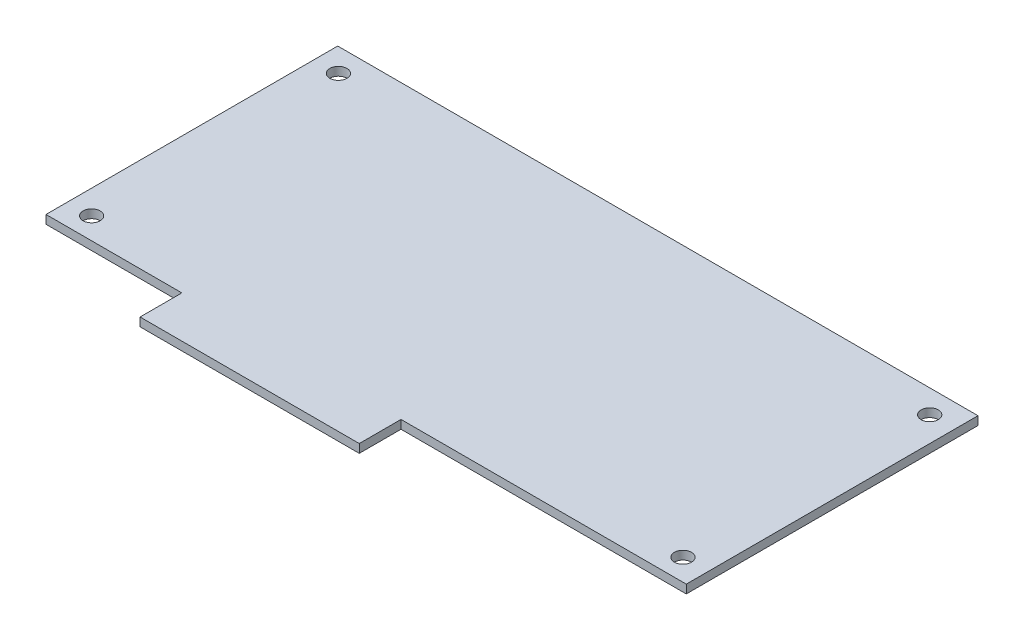
SolidWorks part; units mm, degrees
ref_plane "Front Plane" through (0, 0, 0) normal (0, 0, 1) x (1, 0, 0)
ref_plane "Top Plane" through (0, 0, 0) normal (0, 1, 0) x (1, 0, 0)
ref_plane "Right Plane" through (0, 0, 0) normal (1, 0, 0) x (0, 0, -1)
sketch "Sketch1" plane through (0, 0, 0) normal (0, 1, 0) x (1, 0, 0)
  line L0 (19.558, 31.75) -> (19.558, 36.2756)
  line L1 (60.96, -31.75) -> (-60.96, -31.75)
  line L2 (60.96, -31.75) -> (60.96, 31.75)
  line L3 (60.96, 31.75) -> (-60.96, 31.75)
  line L4 (-60.96, -31.75) -> (-60.96, 31.75)
  line L5 (60.96, -31.75) -> (-60.96, 31.75) construction
  line L6 (60.96, 31.75) -> (-60.96, -31.75) construction
  line L7 (19.558, 36.2756) -> (-17.272, 36.2756)
  line L8 (-17.272, 36.2756) -> (-17.272, 31.75)
  line L9 (1.143, 36.2756) -> (1.143, 31.75) construction
  line L10 (-60.96, -23.7998) -> (-35.092, -23.7998)
  line L11 (-35.092, -23.7998) -> (-35.092, -31.75)
  line L12 (60.96, -23.7998) -> (6.6402, -23.7998)
  line L13 (6.6402, -23.7998) -> (6.6402, -31.75)
  point P0 (0, 0)
  dimension "D1" = 121.92
  dimension "D2" = 63.5
  dimension "D3" = 36.83
  dimension "D4" = 4.5256
  dimension "D5" = 59.817
  dimension "D6" = 55.5498
  dimension "D7" = 41.7322
  dimension "D8" = 25.868
extrude "Boss-Extrude1" add sketch "Sketch1" along normal blind 1.6256 contours L13 L12 L2 L3 L4 L10 L11 L1
hole_wizard "#4 Clearance Hole1" positions "Sketch3" profile "Sketch2" hole size "#4" standard "ANSI Inch"
sketch "Sketch3" plane through (-46.7013, 0, 29.5549) normal (0, -1, 0) x (-1, 0, 0)
  line L1 (9.6867, 56.8599) -> (-102.9115, 56.8599)
  line L2 (9.6867, 9.8699) -> (-102.9115, 9.8699)
  line L6 (-107.6613, 61.3049) -> (14.2587, 61.3049) construction
  line L7 (14.2587, -2.1951) -> (14.2587, 61.3049) construction
  line L9 (-107.6613, -2.1951) -> (-107.6613, 61.3049) construction
  line L10 (-107.6613, 5.7551) -> (-53.3415, 5.7551) construction
  point P9 (-102.9115, 9.8699)
  point P10 (-102.9115, 56.8599)
  point P11 (9.6867, 56.8599)
  point P12 (9.6867, 9.8699)
  dimension "D1" = 4.572
  dimension "D2" = 46.99
  dimension "D3" = 4.7498
  dimension "D4" = 4.445
  dimension "D5" = 4.1148
sketch "Sketch2" plane through (56.2102, 0, 19.685) normal (1, 0, 0) x (0, 0, -1)
  line L0 (0, 0) -> (0, 57.3686)
  line L1 (0, 57.3686) -> (1.6319, 56.388)
  line L2 (1.6319, 56.388) -> (1.6319, 0)
  line L5 (1.6319, 0) -> (0, 0)
  line L10 (0, 57.3686) -> (-1.632, 56.388) construction
  line L11 (0, -6.35) -> (0, 107.95) construction
  dimension "Hole Dia." = 3.2639
  dimension "Hole Depth" = 56.388
  dimension "Drill Angle" = 118
